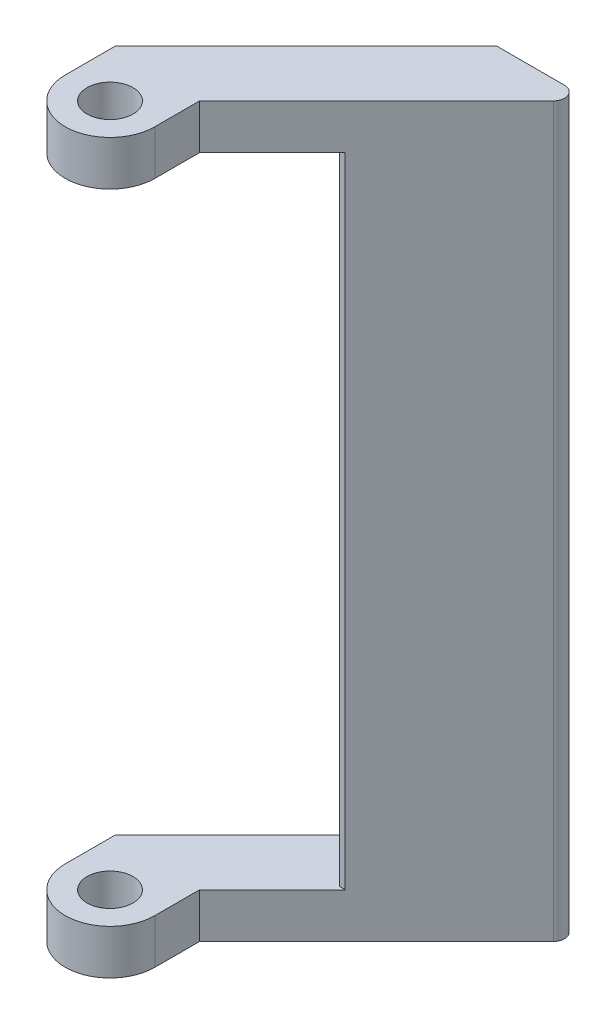
SolidWorks part; units mm, degrees
material "6061 Alloy"
ref_plane "Front Plane" through (0, 0, 0) normal (0, 0, 1) x (1, 0, 0)
ref_plane "Top Plane" through (0, 0, 0) normal (0, 1, 0) x (1, 0, 0)
ref_plane "Right Plane" through (0, 0, 0) normal (1, 0, 0) x (0, 0, -1)
ref_plane "Plane1" through (0, -61.6, 0) normal (0, -1, 0) x (1, 0, 0)
sketch "Sketch1" plane through (0, -61.6, 0) normal (0, -1, 0) x (1, 0, 0)
  line L0 (-25.5, 17.0147) -> (-8.4853, 0)
  line L1 (-8.4853, 0) -> (-2.4142, 0)
  line L2 (-1.7071, 1.7071) -> (-17.5, 17.5)
  line L3 (-17.5, 17.5) -> (-17.5, 21.5)
  line L4 (-25.5, 21.5) -> (-25.5, 17.0147)
  arc A0 (-2.4142, 0) -> (-1.7071, 1.7071) centre (-2.4142, 1) ccw
  arc A1 (-17.5, 21.5) -> (-25.5, 21.5) centre (-21.5, 21.5) ccw
extrude "Boss-Extrude1" add sketch "Sketch1" against normal blind 4
sketch "Sketch2" plane through (0, -57.6, 0) normal (0, 1, 0) x (-1, 0, 0)
  line L0 (1.7071, 1.7071) -> (11, 11)
  line L1 (11, 11) -> (11.5, 11)
  line L2 (11.5, 11) -> (11.5, 3.0147)
  line L3 (11.5, 3.0147) -> (8.4853, 0)
  line L4 (8.4853, 0) -> (2.4142, 0)
  arc A0 (2.4142, 0) -> (1.7071, 1.7071) centre (2.4142, 1) cw
extrude "Boss-Extrude2" add sketch "Sketch2" along normal blind 57
sketch "Sketch3" plane through (0, -0.6, 0) normal (0, 1, 0) x (-1, 0, 0)
  line L0 (8.4853, 0) -> (2.4142, 0)
  line L1 (1.7071, 1.7071) -> (17.5, 17.5)
  line L2 (17.5, 17.5) -> (17.5, 21.5)
  line L3 (25.5, 21.5) -> (25.5, 17.0147)
  line L4 (25.5, 17.0147) -> (8.4853, 0)
  arc A0 (2.4142, 0) -> (1.7071, 1.7071) centre (2.4142, 1) cw
  arc A1 (17.5, 21.5) -> (25.5, 21.5) centre (21.5, 21.5) cw
extrude "Boss-Extrude3" add sketch "Sketch3" along normal blind 4
hole_wizard "Ø4.1 (4.1) Diameter Hole1" positions "Sketch5" profile "Sketch4" hole size "Ø4.1" standard "ANSI Metric"
sketch "Sketch5" plane through (0, 3.4, 0) normal (0, 1, 0) x (1, 0, 0)
  point P0 (-21.5, -21.5)
sketch "Sketch4" plane through (-21.5, 3.4, 21.5) normal (1, 0, 0) x (0, 0, 1)
  line L0 (0, 0) -> (0, 4)
  line L1 (0, 4) -> (2.05, 4)
  line L2 (2.05, 4) -> (2.05, 0)
  line L5 (2.05, 0) -> (0, 0)
  line L11 (0, -6.35) -> (0, 107.95) construction
  dimension "Thru Hole Dia." = 4.1
  dimension "Thru Hole Depth" = 4
hole_wizard "Ø4.1 (4.1) Diameter Hole2" positions "Sketch7" profile "Sketch6" hole size "Ø4.1" standard "ANSI Metric"
sketch "Sketch7" plane through (0, -61.6, 0) normal (0, -1, 0) x (-1, 0, 0)
  point P0 (21.5, -21.5)
sketch "Sketch6" plane through (-21.5, -61.6, 21.5) normal (1, 0, 0) x (0, 0, -1)
  line L0 (0, 0) -> (0, 65)
  line L1 (0, 65) -> (2.05, 65)
  line L2 (2.05, 65) -> (2.05, 0)
  line L5 (2.05, 0) -> (0, 0)
  line L11 (0, -6.35) -> (0, 107.95) construction
  dimension "Thru Hole Dia." = 4.1
  dimension "Thru Hole Depth" = 65
